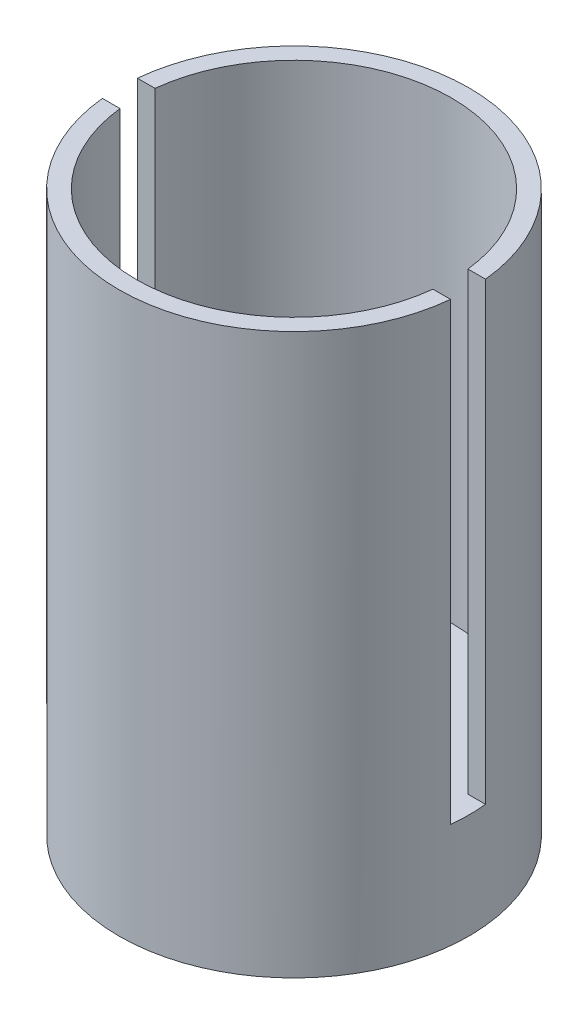
SolidWorks part; units mm, degrees
ref_plane "Front Plane" through (0, 0, 0) normal (0, 0, 1) x (1, 0, 0)
ref_plane "Top Plane" through (0, 0, 0) normal (0, 1, 0) x (1, 0, 0)
ref_plane "Right Plane" through (0, 0, 0) normal (1, 0, 0) x (0, 0, -1)
sketch "Sketch1" plane through (0, 0, 0) normal (0, 1, 0) x (1, 0, 0)
  circle A0 centre (0, 0) radius 25
  circle A1 centre (0, 0) radius 22.5
  dimension "D1" = 50
  dimension "D2" = 45
extrude "Boss-Extrude1" add sketch "Sketch1" along normal blind 80
sketch "Sketch2" plane through (0, 0, 0) normal (0, -1, 0) x (1, 0, 0)
  circle A0 centre (0, 0) radius 25
  circle A1 centre (0, 0) radius 25 construction
extrude "Boss-Extrude2" add sketch "Sketch2" against normal blind 15
sketch "Sketch3" plane through (0, 80, 0) normal (0, 1, 0) x (1, 0, 0)
  line L0 (-25, 0) -> (25, 0) construction
  line L1 (-25, 2.5) -> (25, 2.5)
  line L2 (-25, 2.5) -> (-25, -2.5)
  line L3 (-25, -2.5) -> (25, -2.5)
  line L4 (25, 2.5) -> (25, -2.5)
  line L5 (-25, 0) -> (25, 0) construction
  circle A0 centre (0, 0) radius 25 construction
  dimension "D1" = 2.5
extrude "Cut-Extrude1" cut sketch "Sketch3" against normal up to surface (65 mm away) up to face at (0, 15, -22.5)
sketch "Sketch4" plane through (0, 15, 0) normal (0, 1, 0) x (1, 0, 0)
  circle A0 centre (0, 0) radius 5
  dimension "D1" = 10
extrude "Cut-Extrude2" cut sketch "Sketch4" against normal blind 10
